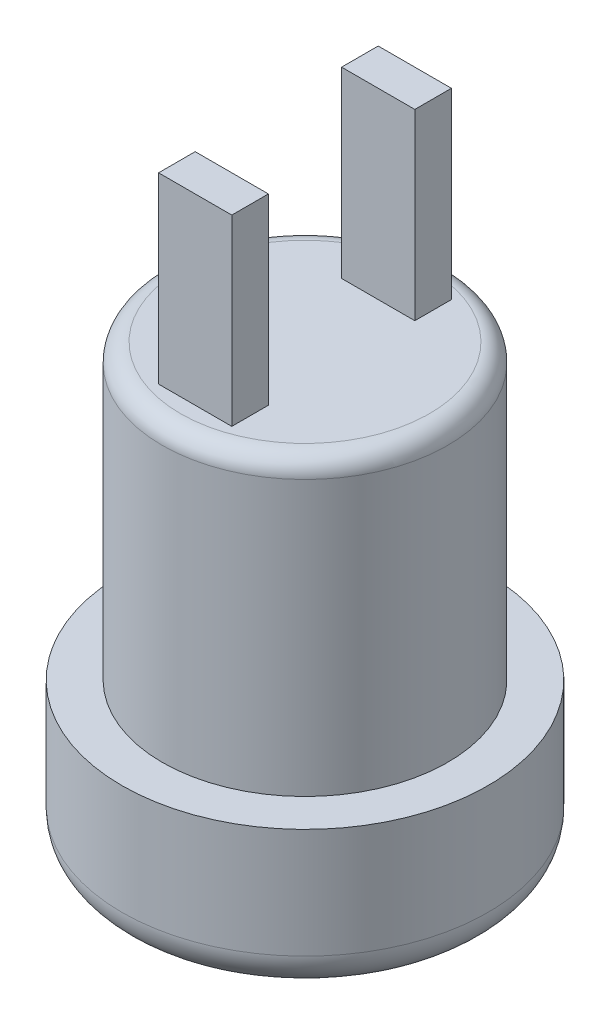
SolidWorks part; units mm, degrees
ref_plane "Plan de face" through (0, 0, 0) normal (0, 0, 1) x (1, 0, 0)
ref_plane "Plan de dessus" through (0, 0, 0) normal (0, 1, 0) x (1, 0, 0)
ref_plane "Plan de droite" through (0, 0, 0) normal (1, 0, 0) x (0, 0, -1)
sketch "Esquisse1" plane through (0, 0, 0) normal (0, 1, 0) x (1, 0, 0)
  circle A0 centre (0, 0) radius 5
  dimension "D1" = 10
extrude "Boss.-Extru.1" add sketch "Esquisse1" along normal blind 4
sketch "Esquisse2" plane through (0, 4, 0) normal (0, 1, 0) x (1, 0, 0)
  circle A0 centre (0, 0) radius 3.9
  dimension "D1" = 7.8
extrude "Boss.-Extru.2" add sketch "Esquisse2" along normal blind 8
fillet "Congé1" radius 1 1 edges at (0, 0, 5)
sketch "Esquisse3" plane through (0, 0, 0) normal (0, -1, 0) x (1, 0, 0)
  circle A0 centre (0, 0) radius 4
  circle A1 centre (0, 0) radius 3
  dimension "D1" = 1
extrude "Enlèv. mat.-Extru.2" cut sketch "Esquisse3" against normal blind 6 contours A1
sketch "Esquisse4" plane through (0, 12, 0) normal (0, 1, 0) x (1, 0, 0)
  line L0 (3.9, 0) -> (-3.9, 0) construction
  line L1 (1, -3) -> (-1, -3)
  line L2 (1, -3) -> (1, -2)
  line L3 (1, -2) -> (-1, -2)
  line L4 (-1, -3) -> (-1, -2)
  line L5 (-1, 3) -> (-1, 2)
  line L6 (1, 2) -> (-1, 2)
  line L7 (1, 3) -> (1, 2)
  line L8 (1, 3) -> (-1, 3)
  circle A0 centre (0, 0) radius 3.9 construction
  point P9 (0, -2)
  point P10 (0, 0)
  dimension "D1" = 2
  dimension "D2" = 1
  dimension "D3" = 2
extrude "Boss.-Extru.3" add sketch "Esquisse4" along normal blind 5
fillet "Congé2" radius 0.5 1 edges at (0, 12, 3.9)
